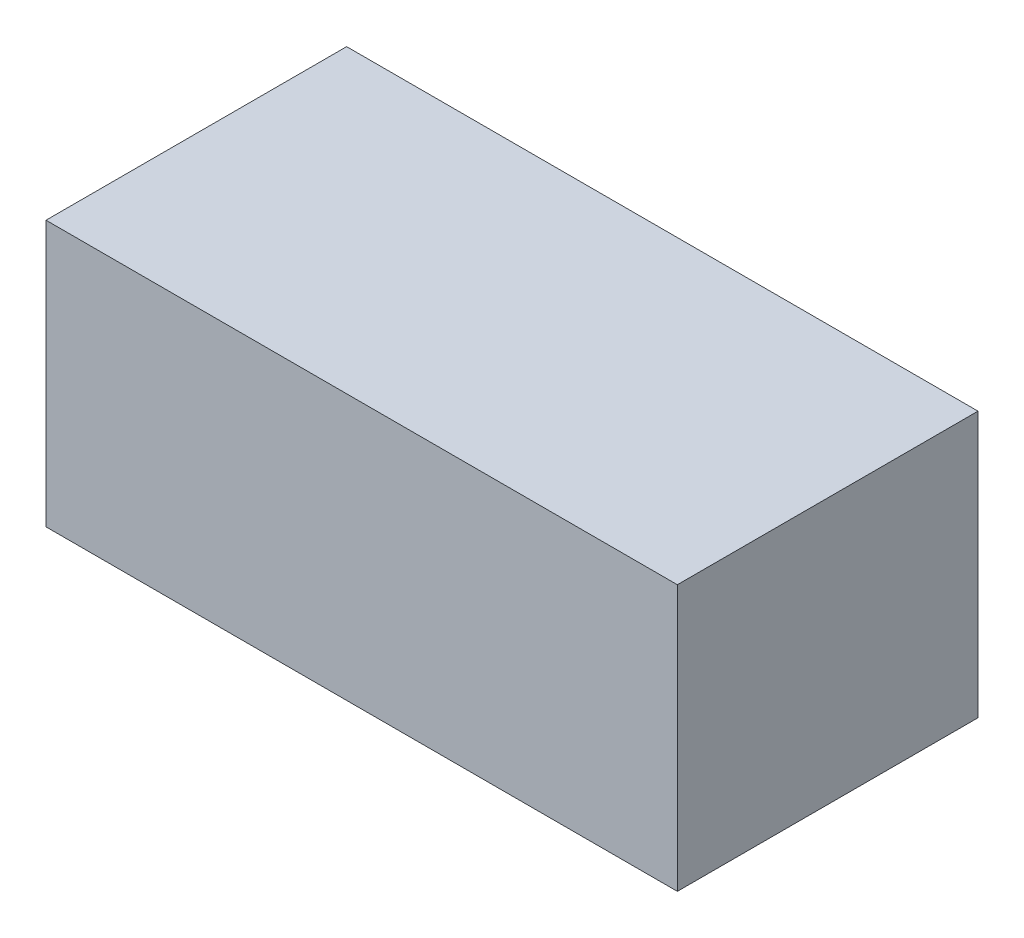
SolidWorks part; units mm, degrees
ref_plane "Front Plane" through (0, 0, 0) normal (0, 0, 1) x (1, 0, 0)
ref_plane "Top Plane" through (0, 0, 0) normal (0, 1, 0) x (1, 0, 0)
ref_plane "Right Plane" through (0, 0, 0) normal (1, 0, 0) x (0, 0, -1)
sketch "Sketch1" plane through (0, 0, 0) normal (0, 1, 0) x (1, 0, 0)
  line L1 (-31.5, 15) -> (31.5, 15)
  line L2 (-31.5, 15) -> (-31.5, -15)
  line L3 (-31.5, -15) -> (31.5, -15)
  line L4 (31.5, 15) -> (31.5, -15)
  line L5 (-31.5, 15) -> (31.5, -15) construction
  line L6 (-31.5, -15) -> (31.5, 15) construction
  point P0 (0, 0)
  dimension "D1" = 30
  dimension "D2" = 63
extrude "Boss-Extrude1" add sketch "Sketch1" along normal blind 26.5
